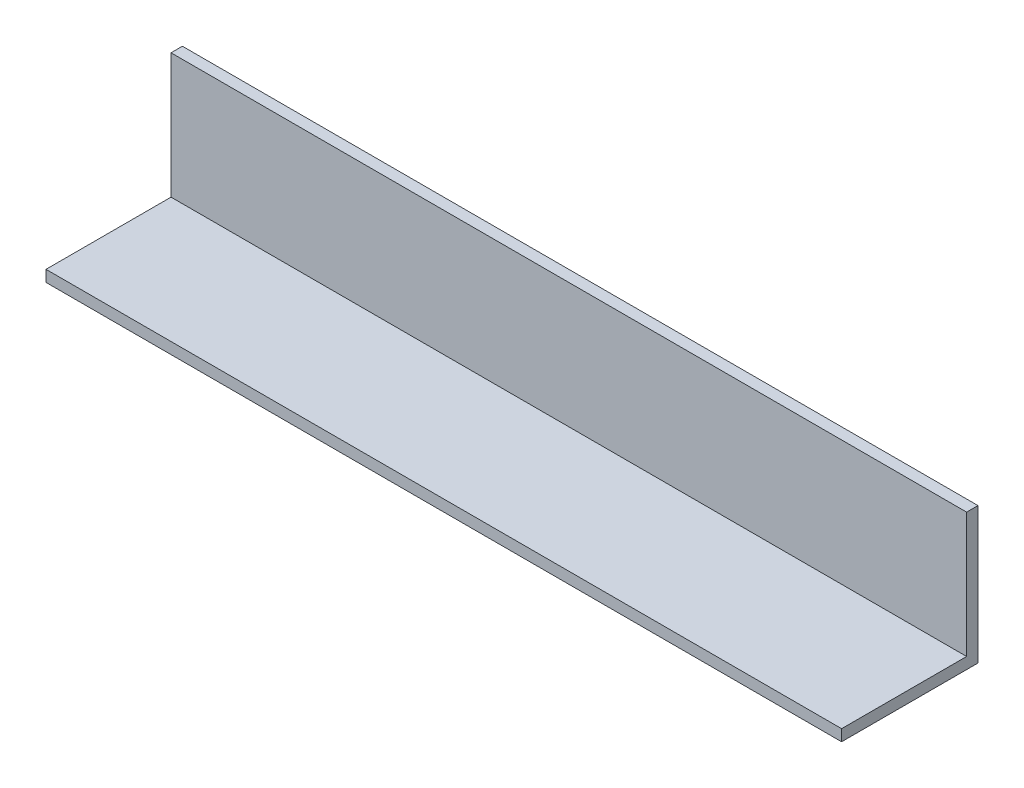
SolidWorks part; units mm, degrees
ref_plane "Front Plane" through (0, 0, 0) normal (0, 0, 1) x (1, 0, 0)
ref_plane "Top Plane" through (0, 0, 0) normal (0, 1, 0) x (1, 0, 0)
ref_plane "Right Plane" through (0, 0, 0) normal (1, 0, 0) x (0, 0, -1)
sketch "Sketch1" plane through (0, 0, 0) normal (0, 0, 1) x (1, 0, 0)
  line L1 (-36.8128, 22.6455) -> (185.4372, 22.6455)
  line L2 (-36.8128, 22.6455) -> (-36.8128, -15.4545)
  line L3 (-36.8128, -15.4545) -> (185.4372, -15.4545)
  line L4 (185.4372, 22.6455) -> (185.4372, -15.4545)
  dimension "D1" = 38.1
  dimension "D2" = 222.25
extrude "Boss-Extrude1" add sketch "Sketch1" along normal blind 38.1
sketch "Sketch2" plane through (0, 0, 38.1) normal (0, 0, 1) x (1, 0, 0)
  line L0 (185.4372, -15.4545) -> (185.4372, 22.6455) construction
  line L1 (-36.8128, 22.6455) -> (185.4372, 22.6455)
  line L2 (-36.8128, 22.6455) -> (-36.8128, -12.2795)
  line L3 (-36.8128, -12.2795) -> (185.4372, -12.2795)
  line L4 (185.4372, 22.6455) -> (185.4372, -12.2795)
  dimension "D1" = 34.925
extrude "Cut-Extrude1" cut sketch "Sketch2" against normal blind 34.925
